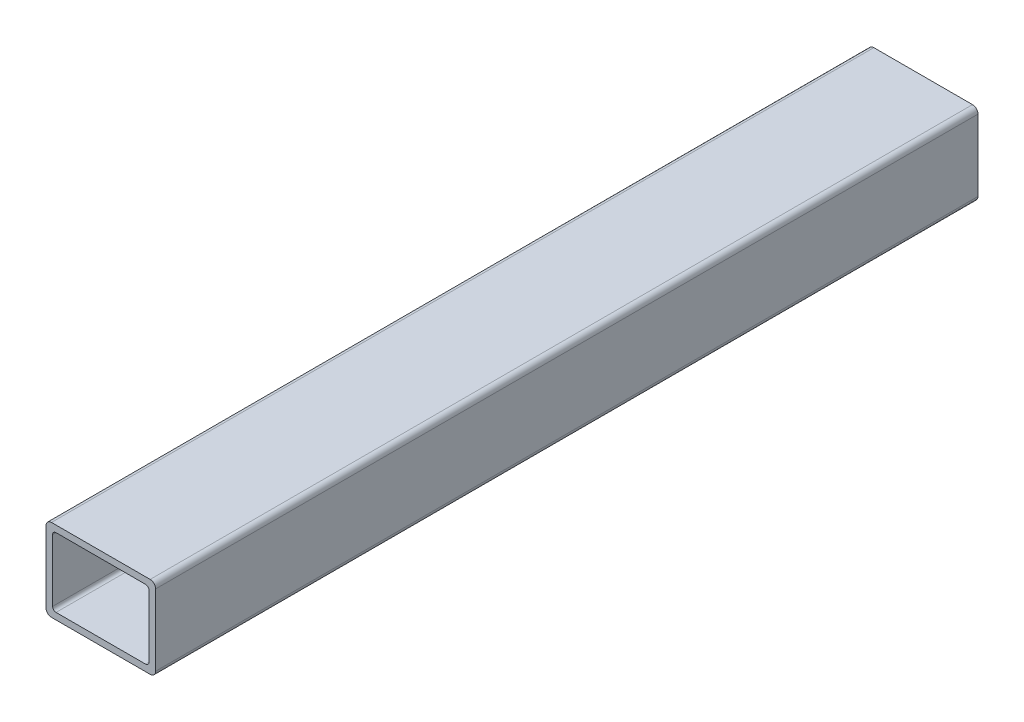
SolidWorks part; units mm, degrees
material "Plain Carbon Steel"
ref_plane "Front" through (0, 0, 0) normal (0, 0, 1) x (1, 0, 0)
ref_plane "Top" through (0, 0, 0) normal (0, 1, 0) x (1, 0, 0)
ref_plane "Right" through (0, 0, 0) normal (1, 0, 0) x (0, 0, -1)
sketch "Sketch1" plane through (0, 0, 0) normal (0, 0, 1) x (1, 0, 0)
  line L0 (-22.352, 0) -> (-25.4, 0) construction
  line L1 (22.86, -19.05) -> (-22.86, -19.05)
  line L2 (25.4, -16.51) -> (25.4, 16.51)
  line L3 (22.86, 19.05) -> (-22.86, 19.05)
  line L4 (-25.4, -16.51) -> (-25.4, 16.51)
  line L5 (25.4, -19.05) -> (-25.4, 19.05) construction
  line L6 (25.4, 19.05) -> (-25.4, -19.05) construction
  line L7 (20.7518, 16.002) -> (-20.7518, 16.002)
  line L8 (22.352, 14.4018) -> (22.352, -14.4018)
  line L9 (20.7518, -16.002) -> (-20.7518, -16.002)
  line L10 (-22.352, 14.4018) -> (-22.352, -14.4018)
  line L11 (22.352, 16.002) -> (-22.352, -16.002) construction
  line L12 (22.352, -16.002) -> (-22.352, 16.002) construction
  line L13 (0, -16.002) -> (0, -19.05) construction
  line L14 (22.352, -14.4018) -> (22.352, -19.05) construction
  line L16 (22.352, -19.05) -> (25.4, -19.05) construction
  arc A0 (-20.7518, -16.002) -> (-22.352, -14.4018) centre (-20.7518, -14.4018) cw
  arc A1 (22.352, -14.4018) -> (20.7518, -16.002) centre (20.7518, -14.4018) cw
  arc A2 (20.7518, 16.002) -> (22.352, 14.4018) centre (20.7518, 14.4018) cw
  arc A3 (-20.7518, 16.002) -> (-22.352, 14.4018) centre (-20.7518, 14.4018) ccw
  arc A4 (22.86, -19.05) -> (25.4, -16.51) centre (22.86, -16.51) ccw
  arc A5 (25.4, 16.51) -> (22.86, 19.05) centre (22.86, 16.51) ccw
  arc A6 (-22.86, 19.05) -> (-25.4, 16.51) centre (-22.86, 16.51) ccw
  arc A7 (-22.86, -19.05) -> (-25.4, -16.51) centre (-22.86, -16.51) cw
  point P0 (0, 0)
  point P6 (0, 0)
  dimension "D2" = 1.6002
  dimension "D3" = 2.54
sketch "Sketch2" plane through (0, 0, 0) normal (1, 0, 0) x (0, 0, -1)
  line L0 (-152.4, 0) -> (152.4, 0) construction
  dimension "Length" = 304.8
ref_plane "Plane1" through (25.4, 0, 0) normal (1, 0, 0) x (0, 0, -1)
sketch "Sketch5" plane through (25.4, 0, 0) normal (1, 0, 0) x (0, 0, -1)
  line L0 (-152.4, 19.05) -> (-152.4, -19.05) construction
  line L1 (152.4, 19.05) -> (152.4, -19.05) construction
sketch "Sketch4" plane through (0, 0, 0) normal (0, 0, 1) x (1, 0, 0)
  line L0 (25.4, -16.51) -> (25.4, 16.51) construction
  line L1 (22.86, 19.05) -> (-22.86, 19.05) construction
  line L2 (-25.4, -16.51) -> (-25.4, 16.51) construction
  line L3 (22.86, -19.05) -> (-22.86, -19.05) construction
  line L4 (22.352, 14.4018) -> (22.352, -14.4018) construction
  line L5 (20.7518, -16.002) -> (-20.7518, -16.002) construction
  line L6 (-22.352, 14.4018) -> (-22.352, -14.4018) construction
  line L7 (20.7518, 16.002) -> (-20.7518, 16.002) construction
  line L8 (25.4, -16.51) -> (25.4, 16.51)
  line L9 (22.86, 19.05) -> (-22.86, 19.05)
  line L10 (-25.4, -16.51) -> (-25.4, 16.51)
  line L11 (22.86, -19.05) -> (-22.86, -19.05)
  line L12 (22.352, 14.4018) -> (22.352, -14.4018)
  line L13 (20.7518, -16.002) -> (-20.7518, -16.002)
  line L14 (-22.352, 14.4018) -> (-22.352, -14.4018)
  line L15 (20.7518, 16.002) -> (-20.7518, 16.002)
  arc A0 (25.4, 16.51) -> (22.86, 19.05) centre (22.86, 16.51) ccw construction
  arc A1 (-22.86, 19.05) -> (-25.4, 16.51) centre (-22.86, 16.51) ccw construction
  arc A2 (-25.4, -16.51) -> (-22.86, -19.05) centre (-22.86, -16.51) ccw construction
  arc A3 (22.86, -19.05) -> (25.4, -16.51) centre (22.86, -16.51) ccw construction
  arc A4 (20.7518, -16.002) -> (22.352, -14.4018) centre (20.7518, -14.4018) ccw construction
  arc A5 (-22.352, -14.4018) -> (-20.7518, -16.002) centre (-20.7518, -14.4018) ccw construction
  arc A6 (-20.7518, 16.002) -> (-22.352, 14.4018) centre (-20.7518, 14.4018) ccw construction
  arc A7 (22.352, 14.4018) -> (20.7518, 16.002) centre (20.7518, 14.4018) ccw construction
  arc A8 (25.4, 16.51) -> (22.86, 19.05) centre (22.86, 16.51) ccw
  arc A9 (-22.86, 19.05) -> (-25.4, 16.51) centre (-22.86, 16.51) ccw
  arc A10 (-25.4, -16.51) -> (-22.86, -19.05) centre (-22.86, -16.51) ccw
  arc A11 (22.86, -19.05) -> (25.4, -16.51) centre (22.86, -16.51) ccw
  arc A12 (20.7518, -16.002) -> (22.352, -14.4018) centre (20.7518, -14.4018) ccw
  arc A13 (-22.352, -14.4018) -> (-20.7518, -16.002) centre (-20.7518, -14.4018) ccw
  arc A14 (-20.7518, 16.002) -> (-22.352, 14.4018) centre (-20.7518, 14.4018) ccw
  arc A15 (22.352, 14.4018) -> (20.7518, 16.002) centre (20.7518, 14.4018) ccw
extrude "Boss-Extrude1" add sketch "Sketch4" along normal blind 381
sketch "Sketch6" plane through (0, 19.05, 0) normal (0, 1, 0) x (1, 0, 0)
  line L0 (0, -381) -> (0, -260.35) construction
  line L2 (-22.86, -260.35) -> (22.86, -260.35) construction
  line L3 (-22.86, 0) -> (-22.86, -381) construction
  line L4 (22.86, 0) -> (22.86, -381) construction
  line L5 (-22.86, -120.65) -> (22.86, -120.65) construction
  line L6 (22.86, -381) -> (-22.86, -381) construction
  line L7 (0, -260.35) -> (0, -120.65) construction
  line L8 (0, -120.65) -> (0, 0) construction
  line L9 (22.86, 0) -> (-22.86, 0) construction
  dimension "D1" = 139.7
equation "\"D3@Sketch1\"=\"Outside Width@Sketch1\"*.05"
equation "\"D2@Sketch1\"=\"D1@Sketch1\"*.05"
